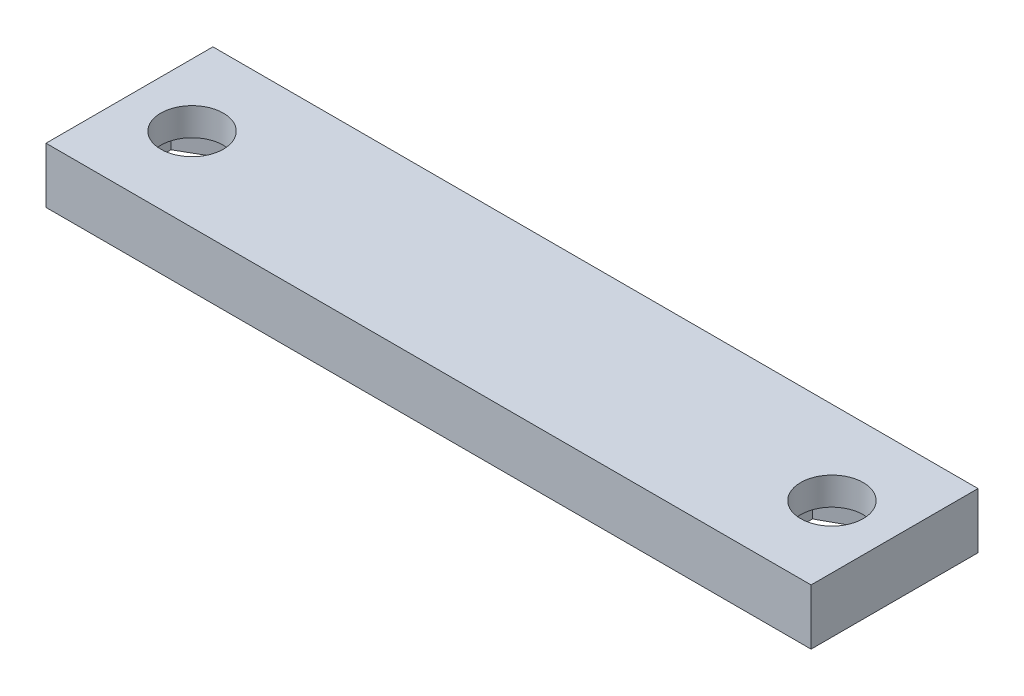
SolidWorks part; units mm, degrees
ref_plane "Front Plane" through (0, 0, 0) normal (0, 0, 1) x (1, 0, 0)
ref_plane "Top Plane" through (0, 0, 0) normal (0, 1, 0) x (1, 0, 0)
ref_plane "Right Plane" through (0, 0, 0) normal (1, 0, 0) x (0, 0, -1)
sketch "Sketch1" plane through (0, 0, 0) normal (0, 1, 0) x (1, 0, 0)
  line L1 (-27.5, 6) -> (27.5, 6)
  line L2 (-27.5, 6) -> (-27.5, -6)
  line L3 (-27.5, -6) -> (27.5, -6)
  line L4 (27.5, 6) -> (27.5, -6)
  line L5 (-27.5, 6) -> (27.5, -6) construction
  line L6 (-27.5, -6) -> (27.5, 6) construction
  circle A0 centre (-23, 0) radius 2.25
  circle A1 centre (23, 0) radius 2.25
  point P0 (0, 0)
  dimension "D3" = 4.5
  dimension "D4" = 4.5
  dimension "D1" = 55
  dimension "D2" = 12
  dimension "D5" = 46
  dimension "D6" = 23
extrude "Boss-Extrude1" add sketch "Sketch1" along normal blind 4
sketch "Sketch2" plane through (0, 0, 0) normal (0, -1, 0) x (-1, 0, 0)
  line L1 (-19.4492, 2.1615) -> (-23.0965, 4.1558)
  line L2 (-23.0965, 4.1558) -> (-26.6473, 1.9943)
  line L3 (-26.6473, 1.9943) -> (-26.5508, -2.1615)
  line L4 (-26.5508, -2.1615) -> (-22.9035, -4.1558)
  line L5 (-22.9035, -4.1558) -> (-19.3527, -1.9943)
  line L6 (-19.3527, -1.9943) -> (-19.4492, 2.1615)
  line L7 (23, 4.1569) -> (19.4, 2.0785)
  line L8 (19.4, 2.0785) -> (19.4, -2.0785)
  line L9 (19.4, -2.0785) -> (23, -4.1569)
  line L10 (23, -4.1569) -> (26.6, -2.0785)
  line L11 (26.6, -2.0785) -> (26.6, 2.0785)
  line L12 (26.6, 2.0785) -> (23, 4.1569)
  circle A0 centre (-23, 0) radius 3.6 construction
  circle A1 centre (23, 0) radius 3.6 construction
  dimension "D1" = 7.2
  dimension "D2" = 7.2
extrude "Cut-Extrude1" cut sketch "Sketch2" against normal blind 2
